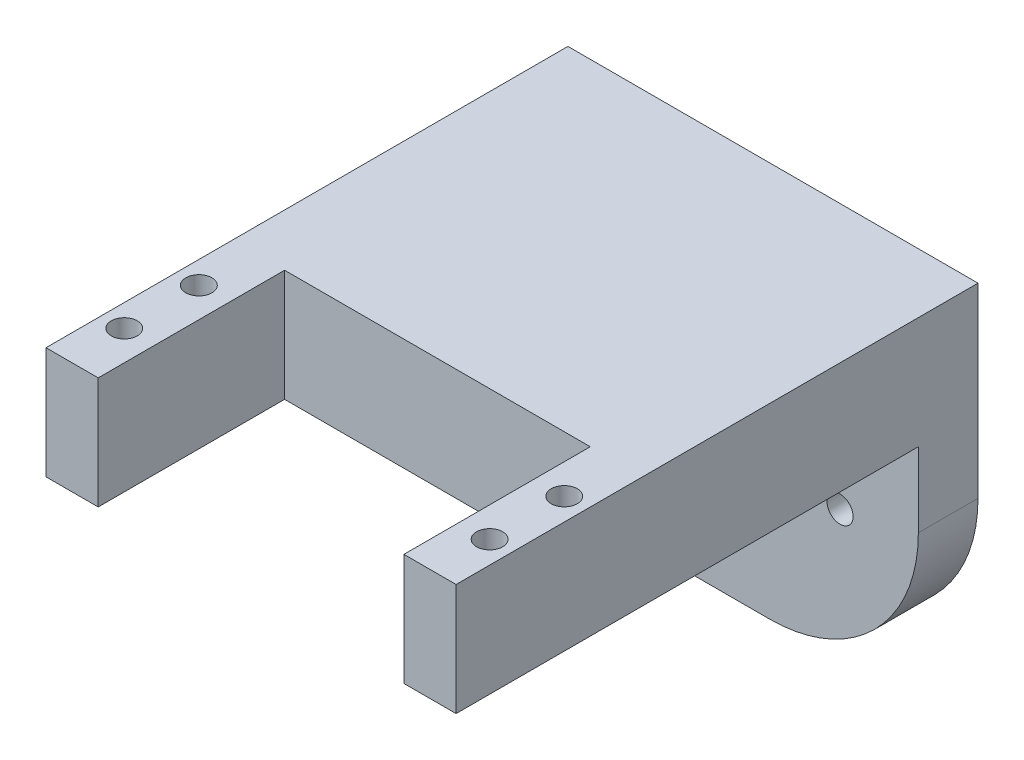
SolidWorks part; units mm, degrees
ref_plane "Front Plane" through (0, 0, 0) normal (0, 0, 1) x (1, 0, 0)
ref_plane "Top Plane" through (0, 0, 0) normal (0, 1, 0) x (1, 0, 0)
ref_plane "Right Plane" through (0, 0, 0) normal (1, 0, 0) x (0, 0, -1)
sketch "Sketch1" plane through (0, 0, 0) normal (0, 0, 1) x (1, 0, 0)
  line L1 (-27.5, 7.5) -> (27.5, 7.5)
  line L2 (-27.5, 7.5) -> (-27.5, -7.5)
  line L3 (-27.5, -7.5) -> (27.5, -7.5)
  line L4 (27.5, 7.5) -> (27.5, -7.5)
  line L5 (-27.5, 7.5) -> (27.5, -7.5) construction
  line L6 (-27.5, -7.5) -> (27.5, 7.5) construction
  point P0 (0, 0)
  dimension "D1" = 55
  dimension "D2" = 15
extrude "Boss-Extrude1" add sketch "Sketch1" along normal blind 70
sketch "Sketch2" plane through (0, 0, 70) normal (0, 0, 1) x (1, 0, 0)
  line L0 (-27.5, -7.5) -> (27.5, -7.5) construction
  line L1 (-20.5, 7.5) -> (20.5, 7.5)
  line L2 (-20.5, 7.5) -> (-20.5, -7.5)
  line L3 (-20.5, -7.5) -> (20.5, -7.5)
  line L4 (20.5, 7.5) -> (20.5, -7.5)
  line L5 (-20.5, 7.5) -> (20.5, -7.5) construction
  line L6 (-20.5, -7.5) -> (20.5, 7.5) construction
  point P0 (0, 0)
  dimension "D1" = 41
extrude "Cut-Extrude1" cut sketch "Sketch2" against normal blind 25
sketch "Sketch3" plane through (0, 7.5, 0) normal (0, 1, 0) x (1, 0, 0)
  line L0 (-24.5, -62.5) -> (24.5, -62.5) construction
  line L1 (0, -62.5) -> (0, 0) construction
  line L2 (-24.5, -52.5) -> (24.5, -52.5) construction
  line L3 (27.5, -70) -> (20.5, -70) construction
  circle A0 centre (-24.5, -62.5) radius 1.75
  circle A1 centre (24.5, -62.5) radius 1.75
  circle A2 centre (-24.5, -52.5) radius 1.75
  circle A3 centre (24.5, -52.5) radius 1.75
  point P7 (0, -62.1808)
  dimension "D2" = 3.5
  dimension "D1" = 49
  dimension "D4" = 49
  dimension "D5" = 7.5
  dimension "D3" = 2
extrude "Cut-Extrude2" cut sketch "Sketch3" against normal through all
sketch "Sketch4" plane through (0, -7.5, 0) normal (0, 1, 0) x (1, 0, 0)
  line L0 (27.5, -70) -> (27.5, 0) construction
  line L1 (-27.5, 0) -> (27.5, 0)
  line L2 (-27.5, 0) -> (-27.5, -8)
  line L3 (-27.5, -8) -> (27.5, -8)
  line L4 (27.5, 0) -> (27.5, -8)
  dimension "D1" = 8
extrude "Boss-Extrude2" add sketch "Sketch4" against normal blind 30
fillet "Fillet1" radius 20 2 edges at (27.5, -37.5, 4) (-27.5, -37.5, 4)
sketch "Sketch5" plane through (0, 0, 0) normal (0, 0, -1) x (-1, 0, 0)
  line L0 (-17, -20) -> (17, -20) construction
  line L1 (-17.4423, -17.5394) -> (-3.3166, -15) construction
  line L2 (-17.4423, -22.4606) -> (-3.3166, -25) construction
  line L3 (3.3166, -25) -> (17.4423, -22.4606) construction
  line L4 (17.4423, -17.5394) -> (3.3166, -15) construction
  line L5 (-3.3166, -15) -> (3.3166, -15) construction
  line L6 (3.3166, -15) -> (3.3166, -25) construction
  line L7 (3.3166, -25) -> (-3.3166, -25) construction
  line L8 (-3.3166, -25) -> (-3.3166, -15) construction
  line L9 (-17.4777, -22.6574) -> (-3.3924, -25.1896)
  line L10 (3.3924, -25.1896) -> (17.4777, -22.6574)
  line L11 (17.4777, -17.3426) -> (3.3924, -14.8104)
  line L12 (-17.4777, -17.3426) -> (-3.3924, -14.8104)
  line L13 (0, 0) -> (0, -20) construction
  arc A0 (-3.3166, -25) -> (3.3166, -25) centre (0, -20) ccw construction
  arc A1 (17.4423, -22.4606) -> (17.4423, -17.5394) centre (17, -20) ccw construction
  arc A2 (-17.4423, -17.5394) -> (-17.4423, -22.4606) centre (-17, -20) ccw construction
  arc A3 (3.3166, -15) -> (-3.3166, -15) centre (0, -20) ccw construction
  arc A4 (-3.3924, -25.1896) -> (3.3924, -25.1896) centre (0, -20) ccw
  arc A5 (17.4777, -22.6574) -> (17.4777, -17.3426) centre (17, -20) ccw
  arc A6 (3.3924, -14.8104) -> (-3.3924, -14.8104) centre (0, -20) ccw
  arc A7 (-17.4777, -17.3426) -> (-17.4777, -22.6574) centre (-17, -20) ccw
  dimension "D1" = 12
  dimension "D2" = 5
  dimension "D3" = 34
  dimension "D4" = 10
  dimension "D5" = 20
extrude "Cut-Extrude3" cut sketch "Sketch5" against normal blind 3
sketch "Sketch6" plane through (0, 0, 3) normal (0, 0, -1) x (-1, 0, 0)
  circle A0 centre (0, -20) radius 1.75
  circle A1 centre (17, -20) radius 1.75
  circle A2 centre (-17, -20) radius 1.75
  dimension "D1" = 3.5
extrude "Cut-Extrude4" cut sketch "Sketch6" against normal through all
